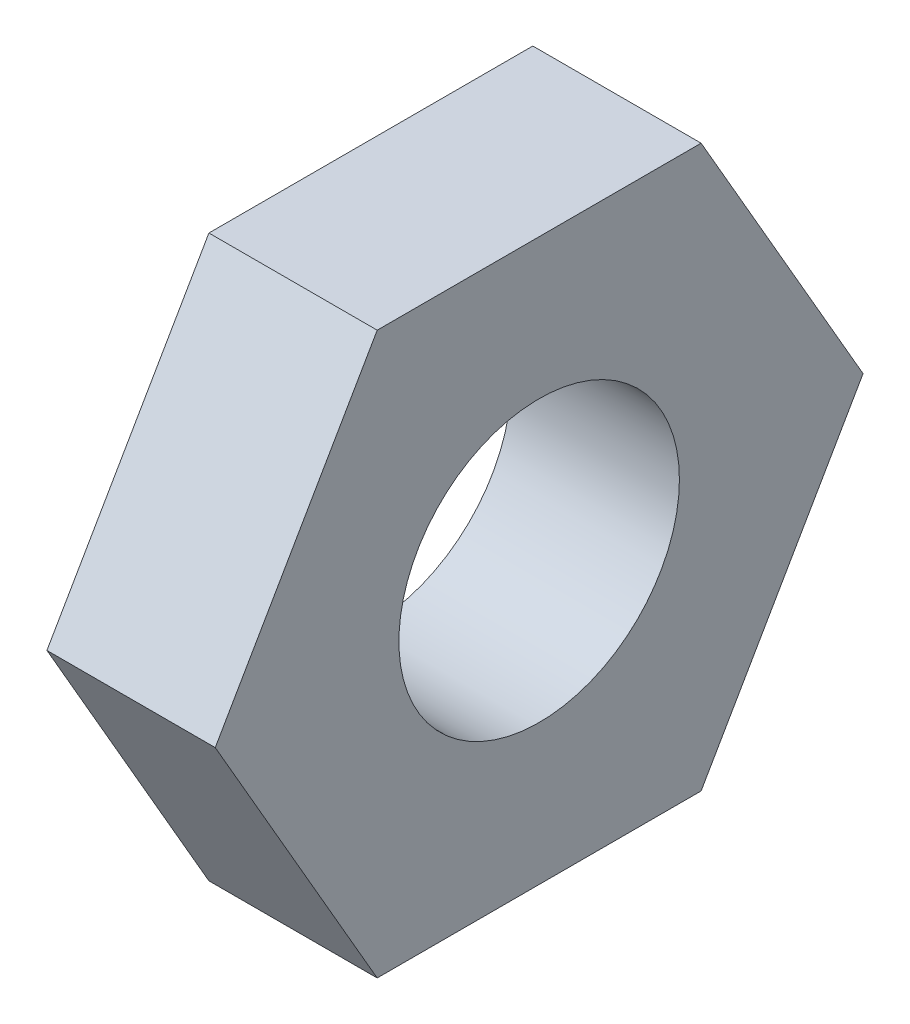
SolidWorks part; units mm, degrees
ref_plane "Front Plane" through (0, 0, 0) normal (0, 0, 1) x (1, 0, 0)
ref_plane "Top Plane" through (0, 0, 0) normal (0, 1, 0) x (1, 0, 0)
ref_plane "Right Plane" through (0, 0, 0) normal (1, 0, 0) x (0, 0, -1)
sketch "Sketch1" plane through (0, 0, 0) normal (1, 0, 0) x (0, 0, -1)
  line L1 (5.7735, 0) -> (2.8868, 5)
  line L2 (2.8868, 5) -> (-2.8868, 5)
  line L3 (-2.8868, 5) -> (-5.7735, 0)
  line L4 (-5.7735, 0) -> (-2.8868, -5)
  line L5 (-2.8868, -5) -> (2.8868, -5)
  line L6 (2.8868, -5) -> (5.7735, 0)
  circle A0 centre (0, 0) radius 5 construction
  circle A1 centre (0, 0) radius 2.5
  dimension "D1" = 10
  dimension "D2" = 5
extrude "Boss-Extrude1" add sketch "Sketch1" along normal blind 3
scale "Scale1" scale about origin uniform scaling yes scale factor 0.5
